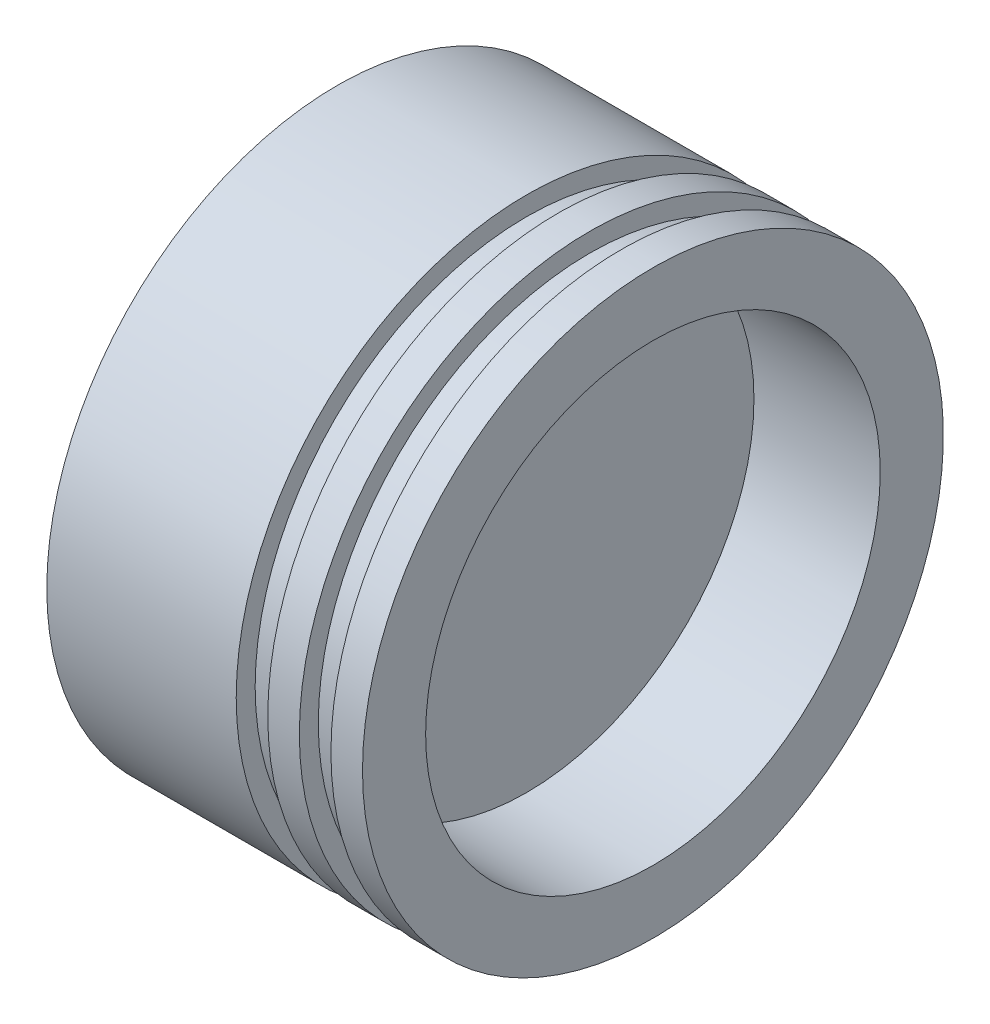
SolidWorks part; units mm, degrees
material "6063-T5"
ref_plane "Front Plane" through (0, 0, 0) normal (0, 0, 1) x (1, 0, 0)
ref_plane "Top Plane" through (0, 0, 0) normal (0, 1, 0) x (1, 0, 0)
ref_plane "Right Plane" through (0, 0, 0) normal (1, 0, 0) x (0, 0, -1)
sketch "Sketch1" plane through (0, 0, 0) normal (0, 0, 1) x (1, 0, 0)
  line L0 (0, 0) -> (30, 0) construction
  line L1 (0, 0) -> (0, 46)
  line L2 (0, 46) -> (30, 46)
  line L7 (30, 46) -> (30, 43)
  line L8 (30, 43) -> (35, 43)
  line L9 (35, 43) -> (35, 46)
  line L10 (35, 46) -> (40, 46)
  line L11 (40, 46) -> (40, 43)
  line L12 (40, 43) -> (45, 43)
  line L13 (45, 43) -> (45, 46)
  line L14 (45, 46) -> (50, 46)
  line L15 (50, 46) -> (50, 36)
  line L16 (50, 36) -> (30, 36)
  line L17 (30, 36) -> (30, 0)
  line L18 (30, 0) -> (0, 0)
  dimension "D1" = 50
  dimension "D2" = 46
  dimension "D3" = 5
  dimension "D4" = 5
  dimension "D5" = 3
  dimension "D7" = 10
  dimension "D8" = 20
revolve "Revolve1" add sketch "Sketch1" angle 360 about L0
